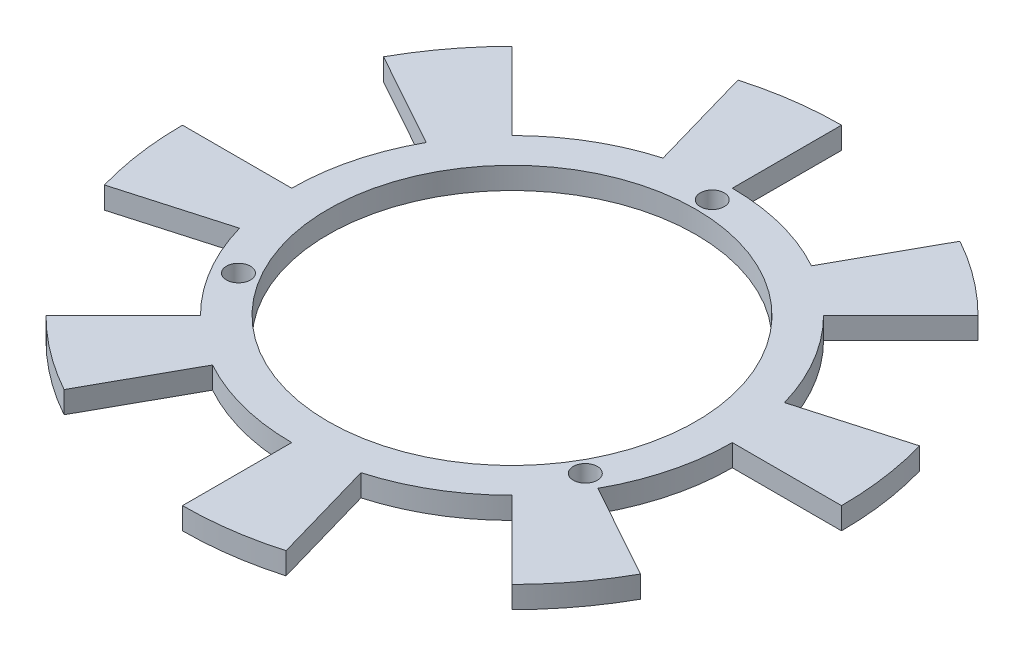
SolidWorks part; units mm, degrees
material "AISI 1010 Steel, hot rolled bar"
ref_plane "Front Plane" through (0, 0, 0) normal (0, 0, 1) x (1, 0, 0)
ref_plane "Top Plane" through (0, 0, 0) normal (0, 1, 0) x (1, 0, 0)
ref_plane "Right Plane" through (0, 0, 0) normal (1, 0, 0) x (0, 0, -1)
sketch "Sketch1" plane through (0, 0, 0) normal (0, 1, 0) x (1, 0, 0)
  circle A0 centre (0, 0) radius 25.25
  dimension "D1" = 50.5
extrude "Extrude-Thin1" add sketch "Sketch1" against normal blind 3 thin
sketch "Sketch2" plane through (0, 0, 0) normal (0, 1, 0) x (1, 0, 0)
  line L0 (0, -30.25) -> (0, 30.25) construction
  line L1 (0, 0) -> (23.8157, -13.75) construction
  line L2 (0, 0) -> (-23.8157, -13.75) construction
  circle A0 centre (0, 27.5) radius 1.65
  circle A1 centre (0, 0) radius 30.25 construction
  circle A4 centre (0, 0) radius 27.5 construction
  circle A7 centre (23.8157, -13.75) radius 1.65
  circle A8 centre (-23.8157, -13.75) radius 1.65
  dimension "D1" = 55
  dimension "D2" = 3.3
  dimension "D3" = 120
  dimension "D4" = 120
extrude "Cut-Extrude3" cut sketch "Sketch2" against normal blind 10
sketch "Sketch5" plane through (0, -3, 0) normal (0, -1, 0) x (1, 0, 0)
  line L0 (0, 0) -> (0, 35.9971) construction
  line L1 (0, 0) -> (9.4011, 32.7855) construction
  line L2 (0, 45.25) -> (0, 30.25)
  line L3 (8.338, 29.0782) -> (12.4726, 43.4971)
  line L4 (31.9966, 31.9966) -> (21.39, 21.39)
  line L5 (26.4572, 14.6655) -> (39.5765, 21.9376)
  line L6 (45.25, 0) -> (30.25, 0)
  line L7 (29.0782, -8.338) -> (43.4971, -12.4726)
  line L8 (31.9966, -31.9966) -> (21.39, -21.39)
  line L9 (14.6655, -26.4572) -> (21.9376, -39.5765)
  line L10 (0, -45.25) -> (0, -30.25)
  line L11 (-8.338, -29.0782) -> (-12.4726, -43.4971)
  line L12 (-31.9966, -31.9966) -> (-21.39, -21.39)
  line L13 (-26.4572, -14.6655) -> (-39.5765, -21.9376)
  line L14 (-45.25, 0) -> (-30.25, 0)
  line L15 (-29.0782, 8.338) -> (-43.4971, 12.4726)
  line L16 (-31.9966, 31.9966) -> (-21.39, 21.39)
  line L17 (-14.6655, 26.4572) -> (-21.9376, 39.5765)
  circle A0 centre (0, 0) radius 30.25 construction
  arc A1 (8.338, 29.0782) -> (0, 30.25) centre (0, 0) ccw
  arc A2 (12.4726, 43.4971) -> (0, 45.25) centre (0, 0) ccw
  arc A3 (39.5765, 21.9376) -> (31.9966, 31.9966) centre (0, 0) ccw
  arc A4 (26.4572, 14.6655) -> (21.39, 21.39) centre (0, 0) ccw
  arc A5 (43.4971, -12.4726) -> (45.25, 0) centre (0, 0) ccw
  arc A6 (29.0782, -8.338) -> (30.25, 0) centre (0, 0) ccw
  arc A7 (21.9376, -39.5765) -> (31.9966, -31.9966) centre (0, 0) ccw
  arc A8 (14.6655, -26.4572) -> (21.39, -21.39) centre (0, 0) ccw
  arc A9 (-12.4726, -43.4971) -> (0, -45.25) centre (0, 0) ccw
  arc A10 (-8.338, -29.0782) -> (0, -30.25) centre (0, 0) ccw
  arc A11 (-39.5765, -21.9376) -> (-31.9966, -31.9966) centre (0, 0) ccw
  arc A12 (-26.4572, -14.6655) -> (-21.39, -21.39) centre (0, 0) ccw
  arc A13 (-43.4971, 12.4726) -> (-45.25, 0) centre (0, 0) ccw
  arc A14 (-29.0782, 8.338) -> (-30.25, 0) centre (0, 0) ccw
  arc A15 (-21.9376, 39.5765) -> (-31.9966, 31.9966) centre (0, 0) ccw
  arc A16 (-14.6655, 26.4572) -> (-21.39, 21.39) centre (0, 0) ccw
  point P87 (0, 0)
  dimension "D2" = 15
  dimension "D1" = 16
  dimension "D3" = 8
extrude "Boss-Extrude1" add sketch "Sketch5" against normal blind 3
